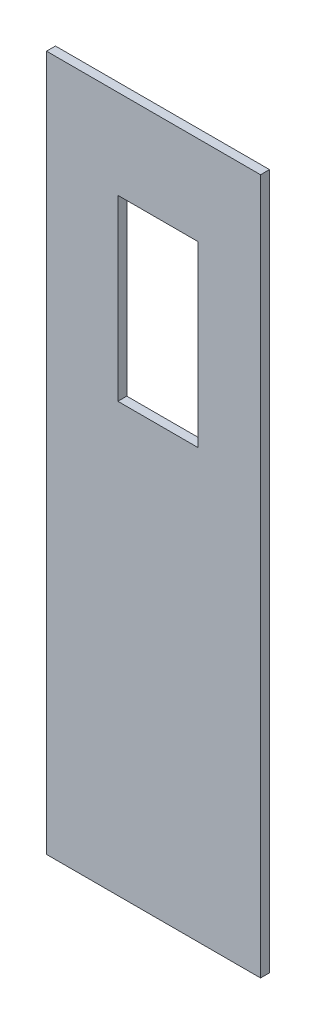
SolidWorks part; units mm, degrees
material "ABS"
ref_plane "Alzado" through (0, 0, 0) normal (0, 0, 1) x (1, 0, 0)
ref_plane "Planta" through (0, 0, 0) normal (0, 1, 0) x (1, 0, 0)
ref_plane "Vista lateral" through (0, 0, 0) normal (1, 0, 0) x (0, 0, -1)
sketch "Croquis1" plane through (0, 0, 0) normal (0, 0, 1) x (1, 0, 0)
  line L1 (-61.0528, 64.6213) -> (58.9472, 64.6213)
  line L2 (-61.0528, 64.6213) -> (-61.0528, -325.3787)
  line L3 (-61.0528, -325.3787) -> (58.9472, -325.3787)
  line L4 (58.9472, 64.6213) -> (58.9472, -325.3787)
  line L5 (-21.0528, -85.3787) -> (23.9472, -85.3787)
  line L6 (-21.0528, -85.3787) -> (-21.0528, 14.6213)
  line L7 (-21.0528, 14.6213) -> (23.9472, 14.6213)
  line L8 (23.9472, -85.3787) -> (23.9472, 14.6213)
  dimension "D1" = 120
  dimension "D2" = 390
  dimension "D3" = 100
  dimension "D4" = 45
  dimension "D5" = 50
  dimension "D6" = 40
extrude "Saliente-Extruir1" add sketch "Croquis1" along normal blind 5
